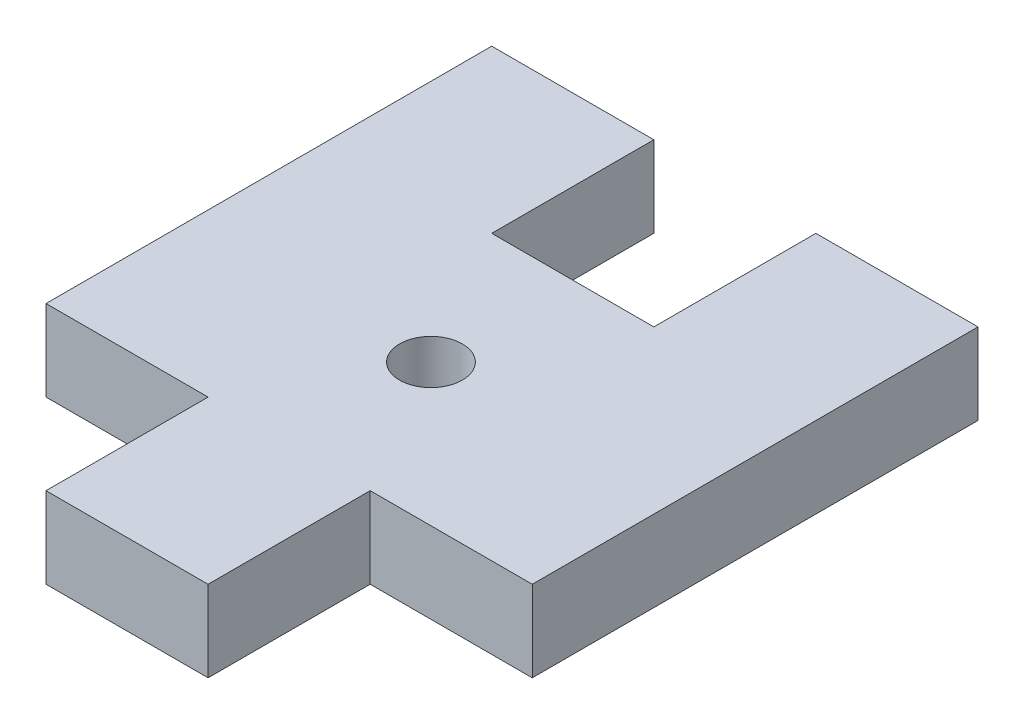
SolidWorks part; units mm, degrees
ref_plane "前基準面" through (0, 0, 0) normal (0, 0, 1) x (1, 0, 0)
ref_plane "上基準面" through (0, 0, 0) normal (0, 1, 0) x (1, 0, 0)
ref_plane "右基準面" through (0, 0, 0) normal (1, 0, 0) x (0, 0, -1)
ref_plane "平面1" through (0, 4, 0) normal (0, 1, 0) x (1, 0, 0)
sketch "草圖1" plane through (0, 4, 0) normal (0, 1, 0) x (1, 0, 0)
  line L0 (-4, 7) -> (-4, 15)
  line L1 (-4, 15) -> (-12, 15)
  line L2 (-12, 15) -> (-12, -7)
  line L3 (-12, -7) -> (-4, -7)
  line L4 (-4, -7) -> (-4, -15)
  line L5 (-4, -15) -> (4, -15)
  line L6 (4, -15) -> (4, -7)
  line L7 (4, -7) -> (12, -7)
  line L8 (12, -7) -> (12, 15)
  line L9 (12, 15) -> (4, 15)
  line L10 (4, 15) -> (4, 7)
  line L11 (4, 7) -> (-4, 7)
  circle A0 centre (0, 0) radius 1.55
extrude "填料-伸長1" add sketch "草圖1" against normal blind 4
